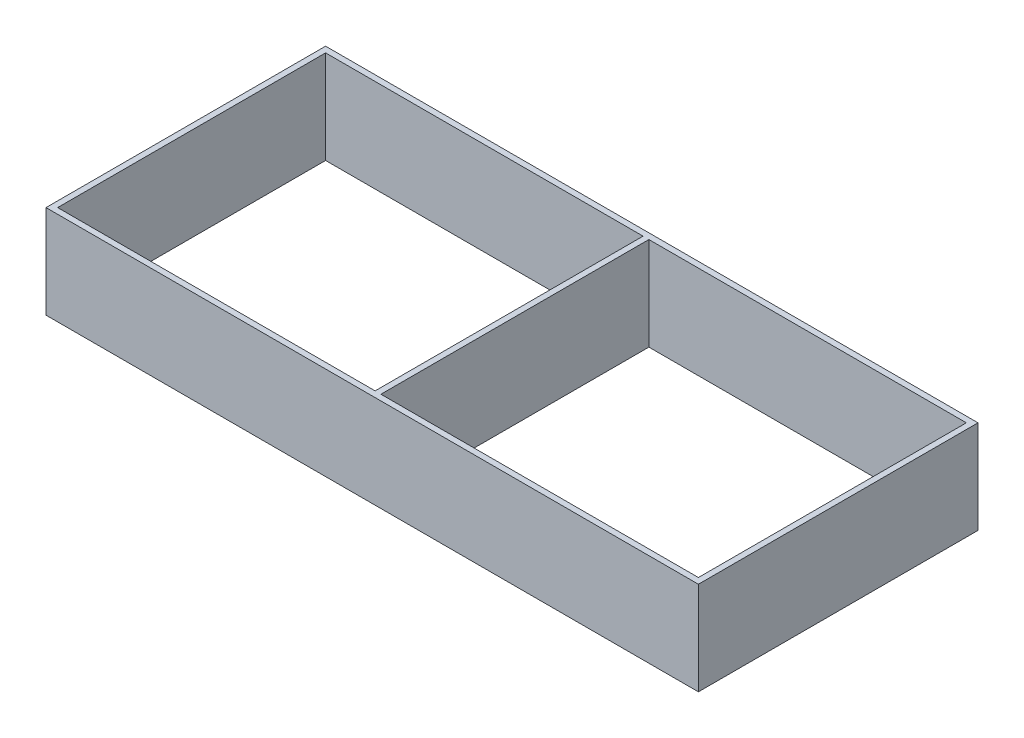
SolidWorks part; units mm, degrees
ref_plane "Front Plane" through (0, 0, 0) normal (0, 0, 1) x (1, 0, 0)
ref_plane "Top Plane" through (0, 0, 0) normal (0, 1, 0) x (1, 0, 0)
ref_plane "Right Plane" through (0, 0, 0) normal (1, 0, 0) x (0, 0, -1)
sketch "Sketch1" plane through (0, 0, 0) normal (0, 1, 0) x (1, 0, 0)
  line L0 (-179.3875, 149.225) -> (-179.3875, 3.175)
  line L1 (0, 0) -> (-355.6, 0)
  line L2 (0, 0) -> (0, 152.4)
  line L3 (0, 152.4) -> (-355.6, 152.4)
  line L4 (-355.6, 0) -> (-355.6, 152.4)
  line L5 (-352.425, 149.225) -> (-179.3875, 149.225)
  line L6 (-352.425, 149.225) -> (-352.425, 3.175)
  line L7 (-352.425, 3.175) -> (-179.3875, 3.175)
  line L8 (-3.175, 149.225) -> (-3.175, 3.175)
  line L9 (-176.2125, 149.225) -> (-176.2125, 3.175)
  line L10 (-177.8, 149.225) -> (-177.8, 3.175) construction
  line L11 (-176.2125, 149.225) -> (-3.175, 149.225)
  line L12 (-176.2125, 3.175) -> (-3.175, 3.175)
  dimension "D1" = 355.6
  dimension "D2" = 152.4
  dimension "D3" = 3.175
  dimension "D4" = 3.175
  dimension "D5" = 3.175
  dimension "D6" = 3.175
  dimension "D7" = 3.175
  dimension "D8" = 1.5875
  dimension "D9" = 177.8
extrude "Boss-Extrude1" add sketch "Sketch1" along normal blind 50.8
